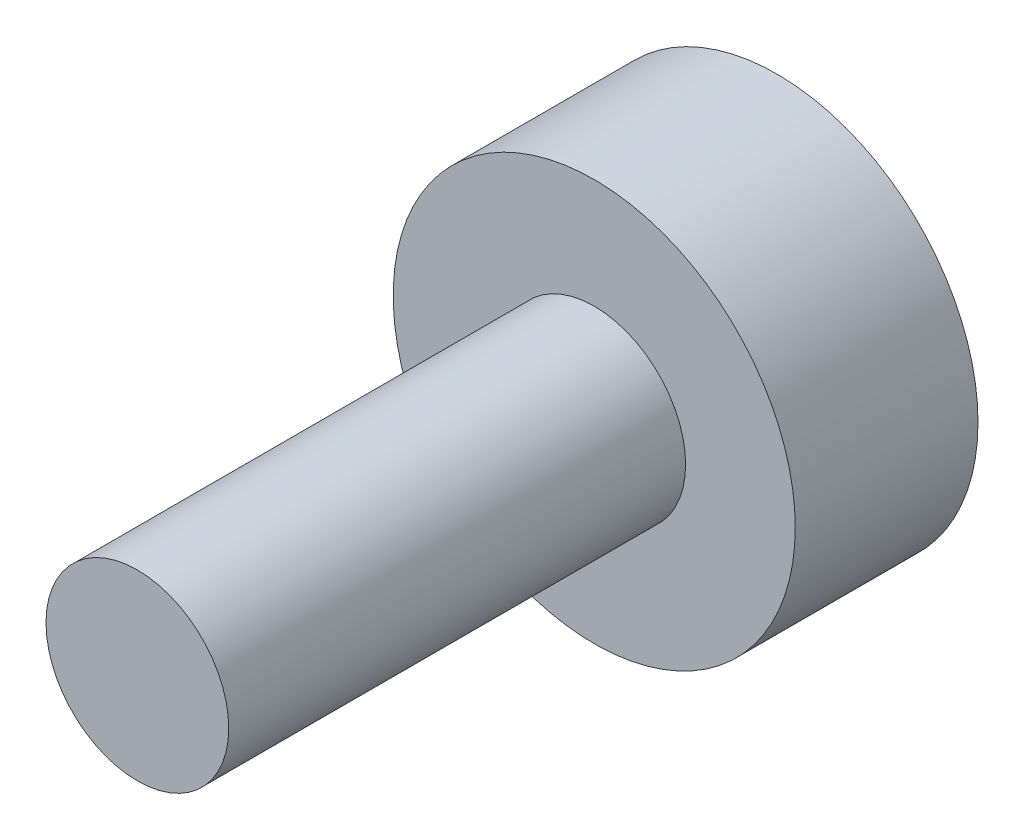
SolidWorks part; units mm, degrees
ref_plane "Front Plane" through (0, 0, 0) normal (0, 0, 1) x (1, 0, 0)
ref_plane "Top Plane" through (0, 0, 0) normal (0, 1, 0) x (1, 0, 0)
ref_plane "Right Plane" through (0, 0, 0) normal (1, 0, 0) x (0, 0, -1)
sketch "Sketch1" plane through (0, 0, 0) normal (0, 0, 1) x (1, 0, 0)
  circle A0 centre (0, 0) radius 11
  dimension "D1" = 22
extrude "Boss-Extrude1" add sketch "Sketch1" along normal blind 10
sketch "Sketch2" plane through (0, 0, 10) normal (0, 0, 1) x (1, 0, 0)
  circle A0 centre (0, 0) radius 5
  dimension "D1" = 10
extrude "Boss-Extrude2" add sketch "Sketch2" along normal blind 25
